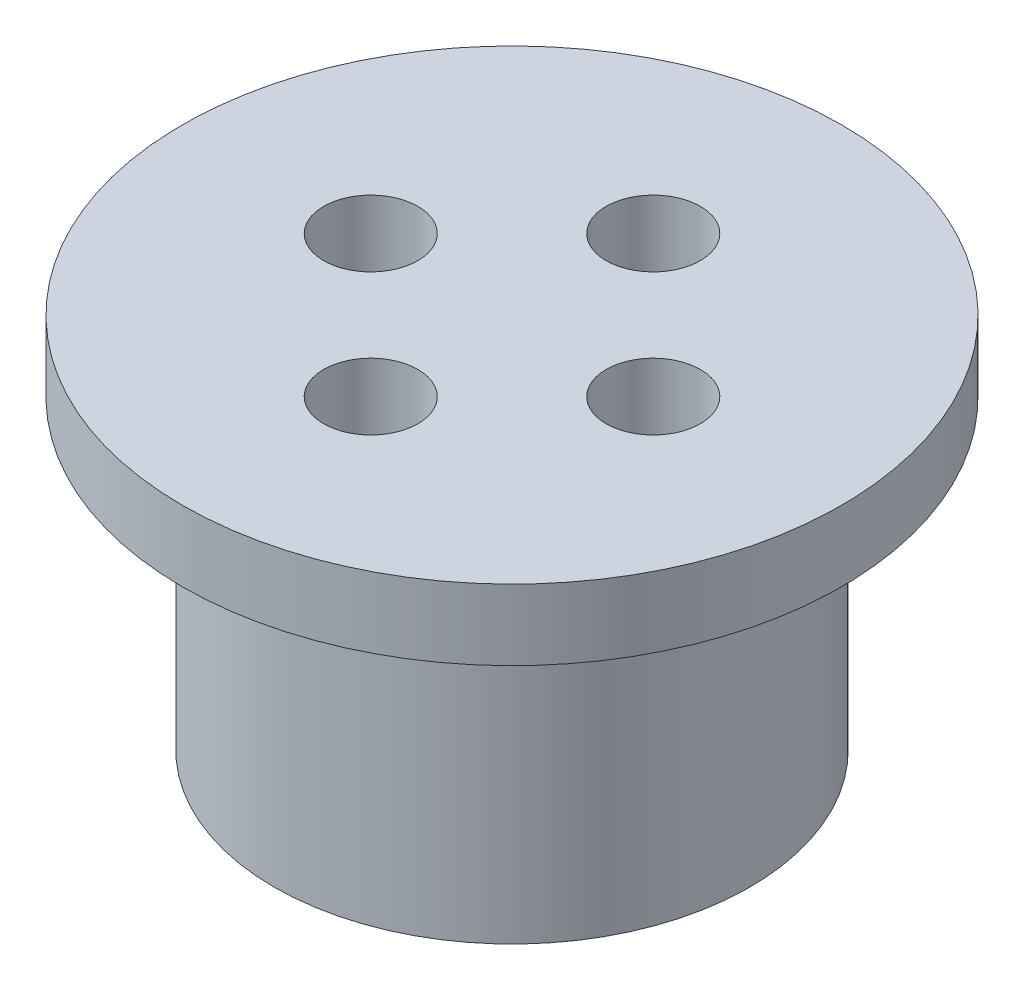
SolidWorks part; units mm, degrees
ref_plane "Front Plane" through (0, 0, 0) normal (0, 0, 1) x (1, 0, 0)
ref_plane "Top Plane" through (0, 0, 0) normal (0, 1, 0) x (1, 0, 0)
ref_plane "Right Plane" through (0, 0, 0) normal (1, 0, 0) x (0, 0, -1)
sketch "Sketch1" plane through (0, 0, 0) normal (0, 1, 0) x (1, 0, 0)
  circle A0 centre (0, 0) radius 10.1
  dimension "D1" = 20.2
extrude "Boss-Extrude1" add sketch "Sketch1" along normal blind 13
sketch "Sketch2" plane through (0, 13, 0) normal (0, 1, 0) x (1, 0, 0)
  circle A0 centre (0, 0) radius 14
extrude "Boss-Extrude2" add sketch "Sketch2" along normal blind 3
sketch "Sketch3" plane through (0, 0, 0) normal (0, -1, 0) x (1, 0, 0)
  circle A0 centre (0, 6) radius 2
  dimension "D1" = 4
  dimension "D2" = 6
extrude "Cut-Extrude1" cut sketch "Sketch3" against normal through all
pattern_circular "CirPattern1" count 4 every 90 about axis through (0, 0, 0) along (0, 1, 0) of "Cut-Extrude1"
